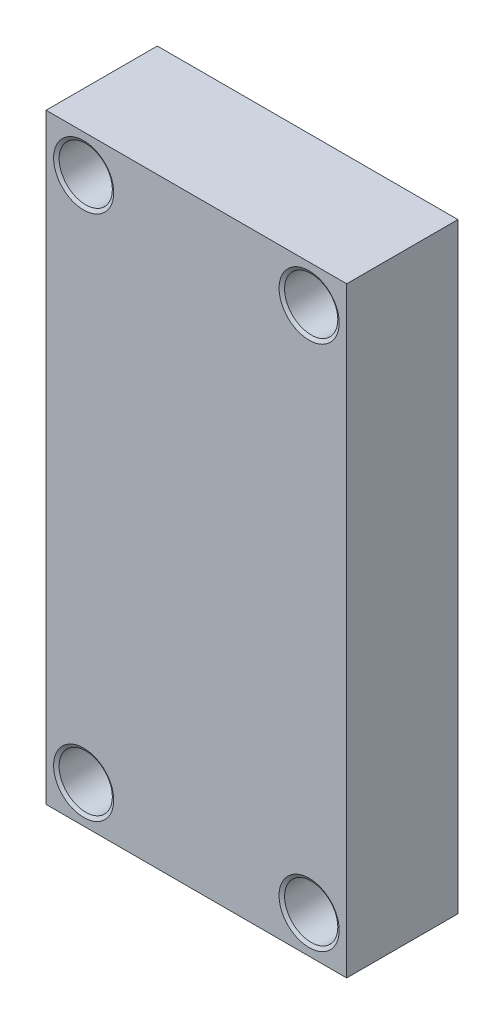
SolidWorks part; units mm, degrees
ref_plane "Front Plane" through (0, 0, 0) normal (0, 0, 1) x (1, 0, 0)
ref_plane "Top Plane" through (0, 0, 0) normal (0, 1, 0) x (1, 0, 0)
ref_plane "Right Plane" through (0, 0, 0) normal (1, 0, 0) x (0, 0, -1)
sketch "Sketch1" plane through (0, 0, 0) normal (0, 0, 1) x (1, 0, 0)
  line L1 (-12.7, 25.4) -> (12.7, 25.4)
  line L2 (-12.7, 25.4) -> (-12.7, -25.4)
  line L3 (-12.7, -25.4) -> (12.7, -25.4)
  line L4 (12.7, 25.4) -> (12.7, -25.4)
  line L5 (-12.7, 25.4) -> (12.7, -25.4) construction
  line L6 (-12.7, -25.4) -> (12.7, 25.4) construction
  point P0 (0, 0)
  dimension "D1" = 50.8
  dimension "D2" = 25.4
extrude "Boss-Extrude1" add sketch "Sketch1" along normal blind 9.398
hole_wizard "#8 Clearance Hole1" positions "Sketch2" profile "Sketch3" hole size "#8" standard "ANSI Inch" end condition through all
sketch "Sketch2" plane through (0, 0, 9.398) normal (0, 0, 1) x (1, 0, 0)
  line L0 (-12.7, -25.4) -> (12.7, -25.4) construction
  line L1 (-12.7, 25.4) -> (-12.7, -25.4) construction
  point P0 (-9.525, -22.225)
  dimension "D1" = 3.175
  dimension "D2" = 3.175
sketch "Sketch3" plane through (-9.525, -22.225, 9.398) normal (1, 0, 0) x (0, -1, 0)
  line L0 (0, 0) -> (0, 9.398)
  line L1 (0, 9.398) -> (2.54, 9.398)
  line L2 (2.2479, 9.2225) -> (2.2479, 0.1755)
  line L3 (2.2479, 0.1755) -> (2.54, 0)
  line L5 (2.54, 0) -> (0, 0)
  line L6 (-2.2479, 0.1755) -> (-2.54, 0) construction
  line L7 (2.54, 9.398) -> (2.2479, 9.2225)
  line L8 (-2.54, 9.398) -> (-2.2479, 9.2225) construction
  line L11 (0, -6.35) -> (0, 107.95) construction
  dimension "Thru Hole Dia." = 4.4958
  dimension "Thru Hole Depth" = 9.398
  dimension "Near C'Sink Dia." = 5.08
  dimension "Near C'Sink Angle" = 118
  dimension "Far C'Sink Dia." = 5.08
  dimension "Far C'Sink Angle" = 118
pattern_linear "LPattern1" count 2 spacing 44.45 along (0, 1, 0) count 2 spacing 19.05 along (1, 0, 0) of "#8 Clearance Hole1"
